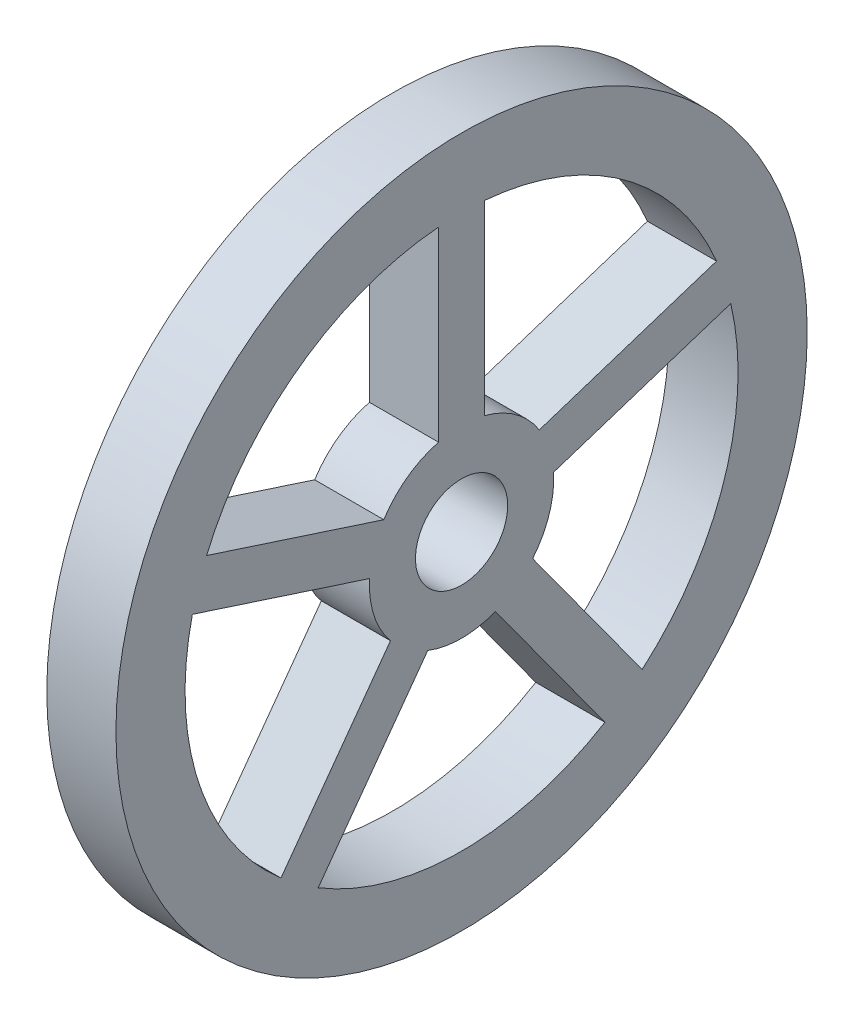
SolidWorks part; units mm, degrees
ref_plane "Front Plane" through (0, 0, 0) normal (0, 0, 1) x (1, 0, 0)
ref_plane "Top Plane" through (0, 0, 0) normal (0, 1, 0) x (1, 0, 0)
ref_plane "Right Plane" through (0, 0, 0) normal (1, 0, 0) x (0, 0, -1)
sketch "Sketch1" plane through (0, 0, 0) normal (1, 0, 0) x (0, 0, -1)
  line L0 (110.6396, 46.4636) -> (33.7441, 21.4787)
  line L2 (-10, 119.5826) -> (-10, 38.7298)
  line L4 (10, 119.5826) -> (10, 38.7298)
  line L5 (116.82, 27.4425) -> (39.9244, 2.4576)
  line L6 (78.3791, -90.8665) -> (30.855, -25.4552)
  line L7 (62.1987, -102.6222) -> (14.6747, -37.2109)
  line L8 (-62.1987, -102.6222) -> (-14.6747, -37.2109)
  line L9 (-78.3791, -90.8665) -> (-30.855, -25.4552)
  line L10 (-116.82, 27.4425) -> (-39.9244, 2.4576)
  line L11 (-110.6396, 46.4636) -> (-33.7441, 21.4787)
  circle A0 centre (0, 0) radius 20
  arc A1 (-39.9244, 2.4576) -> (-30.855, -25.4552) centre (0, 0) ccw
  circle A2 centre (0, 0) radius 150
  arc A3 (-10, 119.5826) -> (-110.6396, 46.4636) centre (0, 0) ccw
  arc A4 (110.6396, 46.4636) -> (10, 119.5826) centre (0, 0) ccw
  arc A5 (-116.82, 27.4425) -> (-78.3791, -90.8665) centre (0, 0) ccw
  arc A6 (-10, 38.7298) -> (-33.7441, 21.4787) centre (0, 0) ccw
  arc A7 (33.7441, 21.4787) -> (10, 38.7298) centre (0, 0) ccw
  arc A8 (30.855, -25.4552) -> (39.9244, 2.4576) centre (0, 0) ccw
  arc A9 (78.3791, -90.8665) -> (116.82, 27.4425) centre (0, 0) ccw
  arc A10 (-62.1987, -102.6222) -> (62.1987, -102.6222) centre (0, 0) ccw
  arc A11 (-14.6747, -37.2109) -> (14.6747, -37.2109) centre (0, 0) ccw
  point P29 (0, 0)
  dimension "D1" = 300
  dimension "D2" = 240
  dimension "D3" = 80
  dimension "D4" = 5
sketch "Sketch2" plane through (0, 0, 0) normal (1, 0, 0) x (0, 0, -1)
extrude "Boss-Extrude1" add sketch "Sketch1" along normal blind 30
